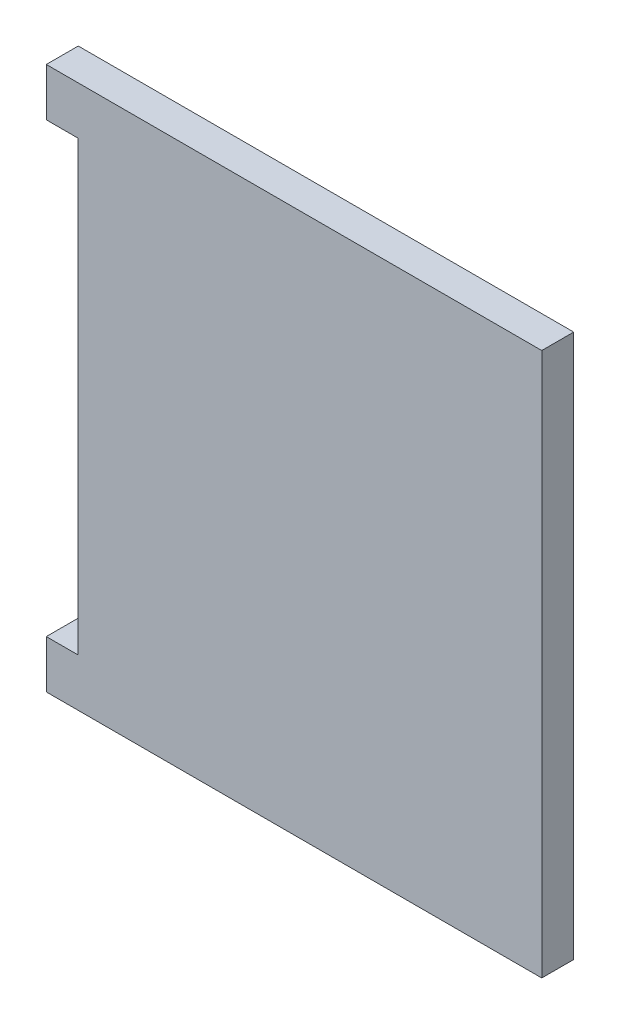
SolidWorks part; units mm, degrees
ref_plane "Front" through (0, 0, 0) normal (0, 0, 1) x (1, 0, 0)
ref_plane "Top" through (0, 0, 0) normal (0, 1, 0) x (1, 0, 0)
ref_plane "Right" through (0, 0, 0) normal (1, 0, 0) x (0, 0, -1)
sketch "Sketch1" plane through (0, 0, 0) normal (0, 0, 1) x (1, 0, 0)
  line L1 (0, 0) -> (196.85, 0)
  line L2 (0, 0) -> (0, -215.9)
  line L3 (0, -215.9) -> (196.85, -215.9)
  line L4 (196.85, 0) -> (196.85, -215.9)
  dimension "D1" = 196.85
  dimension "D2" = 215.9
extrude "Boss-Extrude1" add sketch "Sketch1" along normal blind 12.7
sketch "Sketch2" plane through (0, 0, 0) normal (0, 0, -1) x (-1, 0, 0)
  line L0 (0, 0) -> (0, -215.9) construction
  line L1 (-12.7, -19.05) -> (0, -19.05)
  line L2 (-12.7, -19.05) -> (-12.7, -196.85)
  line L3 (-12.7, -196.85) -> (0, -196.85)
  line L4 (0, -19.05) -> (0, -196.85)
  line L5 (0, -215.9) -> (-196.85, -215.9) construction
  point P6 (0, -107.95)
  dimension "D1" = 12.7
  dimension "D2" = 19.05
extrude "Cut-Extrude1" cut sketch "Sketch2" against normal through all
